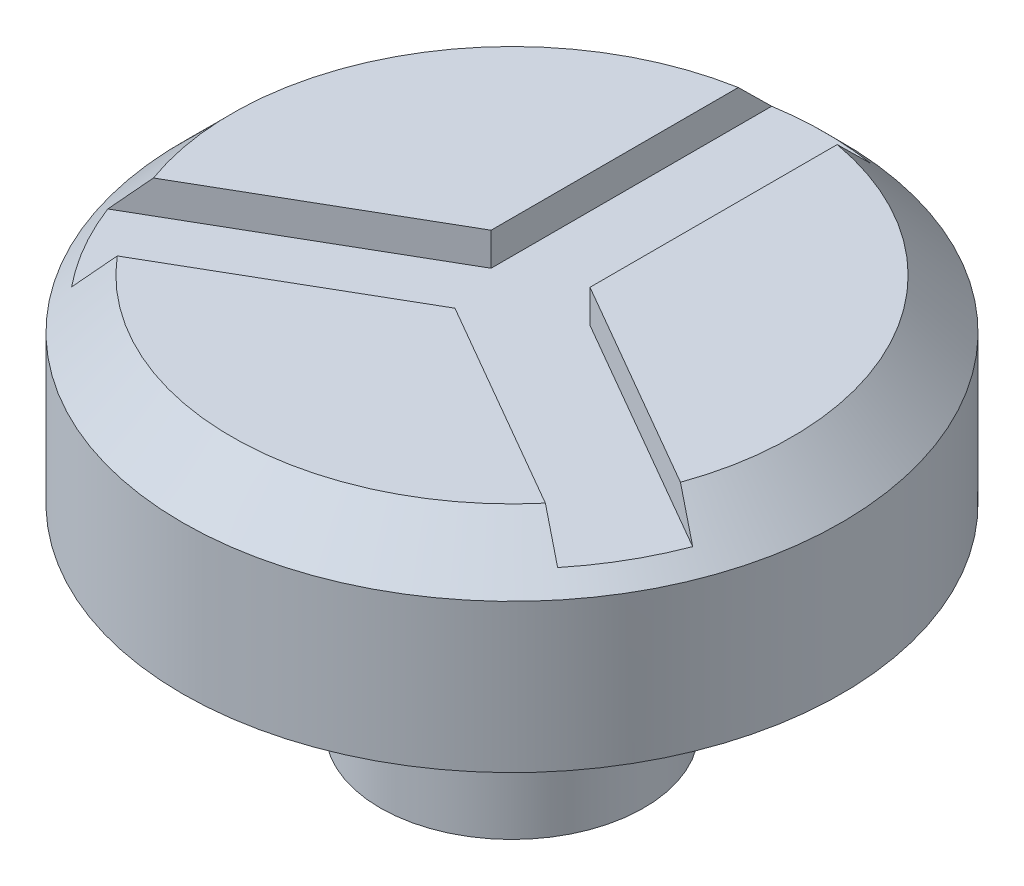
SolidWorks part; units mm, degrees
ref_plane "Front Plane" through (0, 0, 0) normal (0, 0, 1) x (1, 0, 0)
ref_plane "Top Plane" through (0, 0, 0) normal (0, 1, 0) x (1, 0, 0)
ref_plane "Right Plane" through (0, 0, 0) normal (1, 0, 0) x (0, 0, -1)
sketch "Sketch1" plane through (0, 0, 0) normal (0, 1, 0) x (1, 0, 0)
  circle A0 centre (0, 0) radius 20
  dimension "D1" = 40
extrude "Boss-Extrude1" add sketch "Sketch1" along normal blind 30
sketch "Sketch2" plane through (0, 30, 0) normal (0, 1, 0) x (1, 0, 0)
  circle A0 centre (0, 0) radius 50
  dimension "D1" = 100
extrude "Boss-Extrude2" add sketch "Sketch2" along normal blind 30
chamfer "Chamfer1" distance 7.5 angle 45 1 edges at (0, 60, 50)
sketch "Sketch3" plane through (0, 60, 0) normal (0, 1, 0) x (1, 0, 0)
  line L0 (0, 0) -> (0, 50) construction
  line L1 (0, 0) -> (-43.3013, -25) construction
  line L2 (-43.3013, -25) -> (0, 50) construction
  line L3 (-43.3013, -25) -> (43.3013, -25) construction
  line L4 (43.3013, -25) -> (0, 0) construction
  line L5 (0, 50) -> (43.3013, -25) construction
  line L6 (47.0513, -18.5048) -> (7.5, 4.3301)
  line L7 (-7.5, 4.3301) -> (-47.0513, -18.5048)
  line L8 (7.5, 4.3301) -> (7.5, 50)
  line L9 (39.5513, -31.4952) -> (0, -8.6603)
  line L10 (0, -8.6603) -> (-39.5513, -31.4952)
  line L11 (-7.5, 4.3301) -> (-7.5, 50)
  line L12 (39.5513, -31.4952) -> (-3.75, -6.4952) construction
  line L13 (3.75, -6.4952) -> (-39.5513, -31.4952) construction
  line L14 (7.5, 0) -> (7.5, 50) construction
  line L15 (47.0513, -18.5048) -> (3.75, 6.4952) construction
  line L16 (-3.75, 6.4952) -> (-47.0513, -18.5048) construction
  line L17 (-7.5, 0) -> (-7.5, 50) construction
  circle A0 centre (0, 0) radius 50 construction
  arc A1 (47.0513, -18.5048) -> (39.5513, -31.4952) centre (43.3013, -25) cw
  arc A4 (-47.0513, -18.5048) -> (-39.5513, -31.4952) centre (-43.3013, -25) ccw
  arc A6 (7.5, 50) -> (-7.5, 50) centre (0, 50) ccw
  dimension "D1" = 7.5
  dimension "D2" = 7.5
extrude "Cut-Extrude1" cut sketch "Sketch3" against normal blind 5
